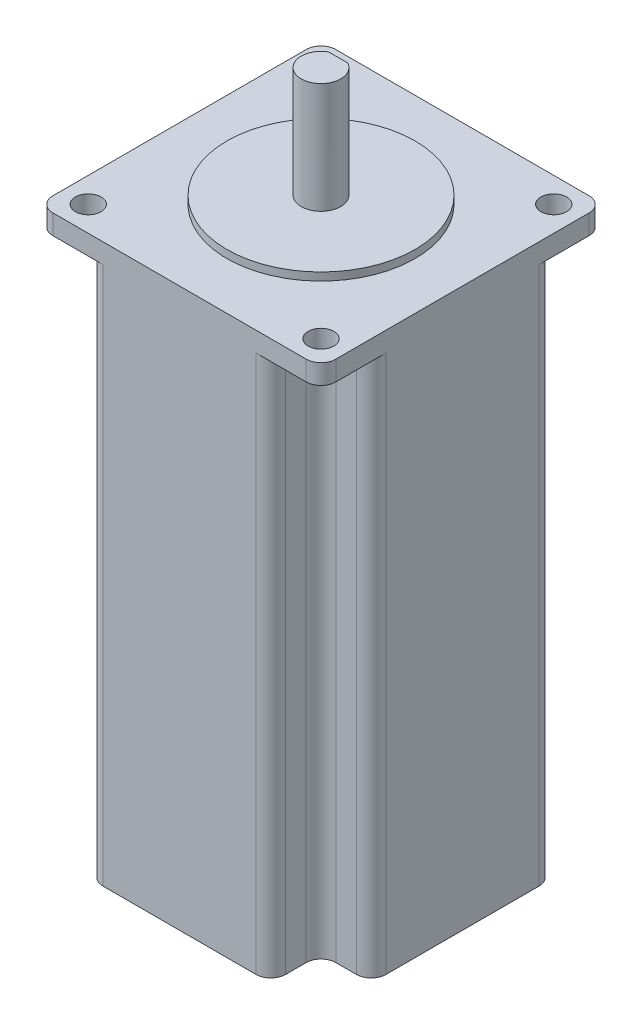
SolidWorks part; units mm, degrees
ref_plane "Front Plane" through (0, 0, 0) normal (0, 0, 1) x (1, 0, 0)
ref_plane "Top Plane" through (0, 0, 0) normal (0, 1, 0) x (1, 0, 0)
ref_plane "Right Plane" through (0, 0, 0) normal (1, 0, 0) x (0, 0, -1)
sketch "Sketch1" plane through (0, 0, 0) normal (0, 1, 0) x (1, 0, 0)
  line L1 (25.65, -28.65) -> (-25.65, -28.65)
  line L2 (28.65, -25.65) -> (28.65, 25.65)
  line L3 (25.65, 28.65) -> (-25.65, 28.65)
  line L4 (-28.65, -25.65) -> (-28.65, 25.65)
  line L5 (28.65, -28.65) -> (-28.65, 28.65) construction
  line L6 (28.65, 28.65) -> (-28.65, -28.65) construction
  arc A0 (-25.65, -28.65) -> (-28.65, -25.65) centre (-25.65, -25.65) cw
  arc A1 (25.65, -28.65) -> (28.65, -25.65) centre (25.65, -25.65) ccw
  arc A2 (28.65, 25.65) -> (25.65, 28.65) centre (25.65, 25.65) ccw
  arc A3 (-25.65, 28.65) -> (-28.65, 25.65) centre (-25.65, 25.65) ccw
  circle A4 centre (-23.57, 23.57) radius 2.6
  circle A5 centre (23.57, 23.57) radius 2.6
  circle A6 centre (23.57, -23.57) radius 2.6
  circle A7 centre (-23.57, -23.57) radius 2.6
  point P0 (0, 0)
  point P26 (0, 0)
  point P27 (0, 0)
  point P28 (0, 0)
  point P29 (24.6718, 24.6718)
  point P30 (0, 0)
  dimension "D2" = 3
  dimension "D3" = 47.14
  dimension "D4" = 5.2
  dimension "D1" = 57.3
extrude "Boss-Extrude1" add sketch "Sketch1" against normal blind 4
sketch "Sketch2" plane through (0, 0, 0) normal (0, 1, 0) x (1, 0, 0)
  circle A0 centre (0, 0) radius 19.05
  dimension "D1" = 38.1
extrude "Boss-Extrude2" add sketch "Sketch2" along normal blind 1.6
sketch "Sketch3" plane through (0, 1.6, 0) normal (0, 1, 0) x (1, 0, 0)
  circle A0 centre (0, 0) radius 4
  dimension "D1" = 8
extrude "Boss-Extrude3" add sketch "Sketch3" along normal offset from surface (22.4 mm away) 24 up to face at (0, 0, -19.05) offset beyond the face yes
sketch "Sketch4" plane through (0, 24, 0) normal (0, 1, 0) x (1, 0, 0)
  line L0 (-1.9365, 3.5) -> (1.9365, 3.5)
  circle A0 centre (0, 0) radius 4 construction
  circle A1 centre (0, 0) radius 4 construction
  arc A2 (1.9365, 3.5) -> (-1.9365, 3.5) centre (0, 0) ccw
  point P6 (0, -4)
  point P7 (0.6713, -3.9433)
  dimension "D1" = 7.5
extrude "Cut-Extrude1" cut sketch "Sketch4" against normal blind 20
sketch "Sketch5" plane through (0, -4, 0) normal (0, -1, 0) x (1, 0, 0)
  line L0 (-18.49, 25.65) -> (-18.49, 21.49)
  line L1 (-25.65, 28.65) -> (25.65, 28.65) construction
  line L2 (-21.49, 18.49) -> (-25.65, 18.49)
  line L3 (-28.65, -25.65) -> (-28.65, 25.65) construction
  line L4 (-28.65, 15.49) -> (-28.65, -15.49)
  line L5 (-25.65, -18.49) -> (-21.49, -18.49)
  line L6 (-18.49, -21.49) -> (-18.49, -25.65)
  line L7 (25.65, -28.65) -> (-25.65, -28.65) construction
  line L8 (-15.49, -28.65) -> (15.49, -28.65)
  line L9 (18.49, -25.65) -> (18.49, -21.49)
  line L10 (21.49, -18.49) -> (25.65, -18.49)
  line L11 (28.65, 25.65) -> (28.65, -25.65) construction
  line L12 (28.65, -15.49) -> (28.65, 15.49)
  line L13 (25.65, 18.49) -> (21.49, 18.49)
  line L14 (18.49, 21.49) -> (18.49, 25.65)
  line L15 (15.49, 28.65) -> (-15.49, 28.65)
  arc A0 (-18.49, 21.49) -> (-21.49, 18.49) centre (-21.49, 21.49) cw
  arc A1 (-25.65, 18.49) -> (-28.65, 15.49) centre (-25.65, 15.49) ccw
  arc A2 (-28.65, -15.49) -> (-25.65, -18.49) centre (-25.65, -15.49) ccw
  arc A3 (-21.49, -18.49) -> (-18.49, -21.49) centre (-21.49, -21.49) cw
  arc A4 (-18.49, -25.65) -> (-15.49, -28.65) centre (-15.49, -25.65) ccw
  arc A5 (15.49, -28.65) -> (18.49, -25.65) centre (15.49, -25.65) ccw
  arc A6 (18.49, -21.49) -> (21.49, -18.49) centre (21.49, -21.49) cw
  arc A7 (25.65, -18.49) -> (28.65, -15.49) centre (25.65, -15.49) ccw
  arc A8 (28.65, 15.49) -> (25.65, 18.49) centre (25.65, 15.49) ccw
  arc A9 (21.49, 18.49) -> (18.49, 21.49) centre (21.49, 21.49) cw
  arc A10 (18.49, 25.65) -> (15.49, 28.65) centre (15.49, 25.65) ccw
  arc A11 (-18.49, 25.65) -> (-15.49, 28.65) centre (-15.49, 25.65) cw
  circle A12 centre (-23.57, 23.57) radius 5.08 construction
  point P24 (-28.65, 18.49)
  point P27 (-28.65, -18.49)
  point P32 (-18.49, -28.65)
  point P35 (18.49, -28.65)
  point P40 (28.65, -18.49)
  point P43 (28.65, 18.49)
  point P48 (18.49, 28.65)
  point P51 (-18.49, 28.65)
  dimension "D1" = 3
extrude "Boss-Extrude4" add sketch "Sketch5" along normal offset from surface (109 mm away) 113 up to face at (0, 0, -19.05)
